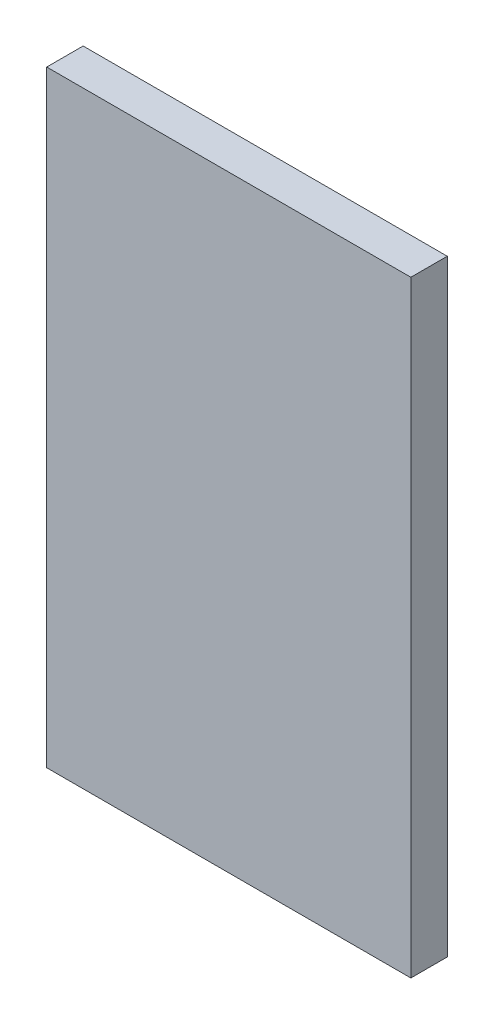
SolidWorks part; units mm, degrees
ref_plane "Plan de face" through (0, 0, 0) normal (0, 0, 1) x (1, 0, 0)
ref_plane "Plan de dessus" through (0, 0, 0) normal (0, 1, 0) x (1, 0, 0)
ref_plane "Plan de droite" through (0, 0, 0) normal (1, 0, 0) x (0, 0, -1)
sketch "Esquisse1" plane through (0, 0, 0) normal (0, 0, 1) x (1, 0, 0)
  line L1 (-79.2794, 43.9702) -> (-49.2794, 43.9702)
  line L2 (-79.2794, 43.9702) -> (-79.2794, -6.0298)
  line L3 (-79.2794, -6.0298) -> (-49.2794, -6.0298)
  line L4 (-49.2794, 43.9702) -> (-49.2794, -6.0298)
  dimension "D1" = 30
  dimension "D2" = 50
extrude "Boss.-Extru.1" add sketch "Esquisse1" along normal blind 3
